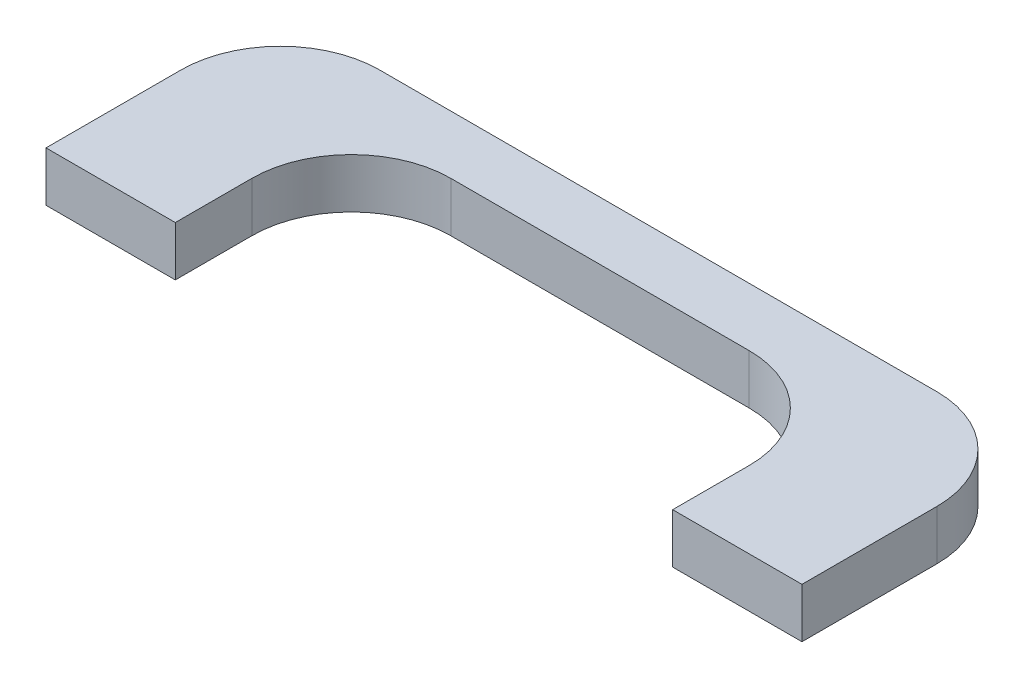
SolidWorks part; units mm, degrees
ref_plane "Alzado" through (0, 0, 0) normal (0, 0, 1) x (1, 0, 0)
ref_plane "Planta" through (0, 0, 0) normal (0, 1, 0) x (1, 0, 0)
ref_plane "Vista lateral" through (0, 0, 0) normal (1, 0, 0) x (0, 0, -1)
sketch "Croquis1" plane through (0, 0, 0) normal (0, 1, 0) x (1, 0, 0)
  line L0 (0, 0) -> (13, 0)
  line L2 (0, 0) -> (0, 13.555)
  line L6 (76, 0) -> (76, 13.555)
  line L7 (10, 23.555) -> (66, 23.555)
  line L9 (13, 0) -> (13, 7.6962)
  line L10 (23, 17.6962) -> (53, 17.6962)
  line L11 (63, 7.6962) -> (63, 0)
  line L12 (76, 0) -> (63, 0)
  line L14 (13, 0) -> (63, 0) construction
  arc A0 (10, 23.555) -> (0, 13.555) centre (10, 13.555) ccw
  arc A1 (66, 23.555) -> (76, 13.555) centre (66, 13.555) cw
  arc A2 (23, 17.6962) -> (13, 7.6962) centre (23, 7.6962) ccw
  arc A3 (63, 7.6962) -> (53, 17.6962) centre (53, 7.6962) ccw
  point P11 (0, 23.555)
  dimension "D6" = 10
  dimension "D2" = 10
  dimension "D3" = 13
  dimension "D4" = 76
  dimension "D7" = 13
  dimension "D8" = 50
extrude "Saliente-Extruir2" add sketch "Croquis1" along normal blind 5
